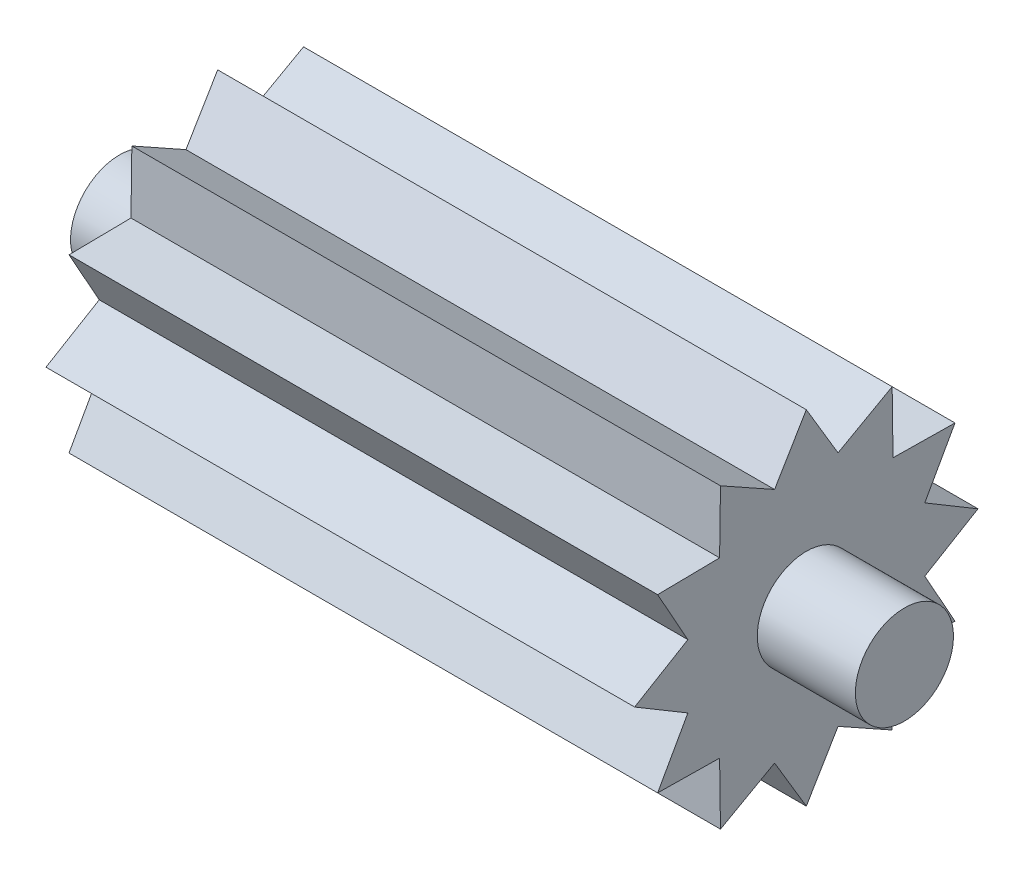
SolidWorks part; units mm, degrees
ref_plane "Front Plane" through (0, 0, 0) normal (0, 0, 1) x (1, 0, 0)
ref_plane "Top Plane" through (0, 0, 0) normal (0, 1, 0) x (1, 0, 0)
ref_plane "Right Plane" through (0, 0, 0) normal (1, 0, 0) x (0, 0, -1)
sketch "Sketch1" plane through (0, 0, 0) normal (1, 0, 0) x (0, 0, -1)
  line L0 (0, 0) -> (0, 10.8328) construction
  line L1 (0, 0) -> (2.9543, 11.0257) construction
  line L2 (0, 8.75) -> (1.6176, 6.037)
  line L3 (0, 8.75) -> (-1.6176, 6.037)
  line L4 (4.375, 7.5777) -> (1.6176, 6.037)
  line L5 (4.375, 7.5777) -> (4.4194, 4.4194)
  line L6 (7.5777, 4.375) -> (4.4194, 4.4194)
  line L7 (7.5777, 4.375) -> (6.037, 1.6176)
  line L8 (8.75, 0) -> (6.037, 1.6176)
  line L9 (8.75, 0) -> (6.037, -1.6176)
  line L10 (7.5777, -4.375) -> (6.037, -1.6176)
  line L11 (7.5777, -4.375) -> (4.4194, -4.4194)
  line L12 (4.375, -7.5777) -> (4.4194, -4.4194)
  line L13 (4.375, -7.5777) -> (1.6176, -6.037)
  line L14 (0, -8.75) -> (1.6176, -6.037)
  line L15 (0, -8.75) -> (-1.6176, -6.037)
  line L16 (-4.375, -7.5777) -> (-1.6176, -6.037)
  line L17 (-4.375, -7.5777) -> (-4.4194, -4.4194)
  line L18 (-7.5777, -4.375) -> (-4.4194, -4.4194)
  line L19 (-7.5777, -4.375) -> (-6.037, -1.6176)
  line L20 (-8.75, 0) -> (-6.037, -1.6176)
  line L21 (-8.75, 0) -> (-6.037, 1.6176)
  line L22 (-7.5777, 4.375) -> (-6.037, 1.6176)
  line L23 (-7.5777, 4.375) -> (-4.4194, 4.4194)
  line L24 (-4.375, 7.5777) -> (-4.4194, 4.4194)
  line L25 (-4.375, 7.5777) -> (-1.6176, 6.037)
  point P3 (0, 8.75)
  point P4 (0, 6.25)
  point P46 (0, 0)
  dimension "D1" = 6.25
  dimension "D2" = 2.5
  dimension "D3" = 15
  dimension "D5" = 6.25
  dimension "D4" = 12
extrude "Boss-Extrude1" add sketch "Sketch1" along normal blind 15
sketch "Sketch4" plane through (15, 0, 0) normal (1, 0, 0) x (0, 0, -1)
  circle A0 centre (0, 0) radius 2.5
  dimension "D1" = 5
extrude "Boss-Extrude3" add sketch "Sketch4" along normal blind 5
mirror "Mirror1" about plane through (0, 0, 0) normal (1, 0, 0) of "Boss-Extrude1", "Boss-Extrude3"
